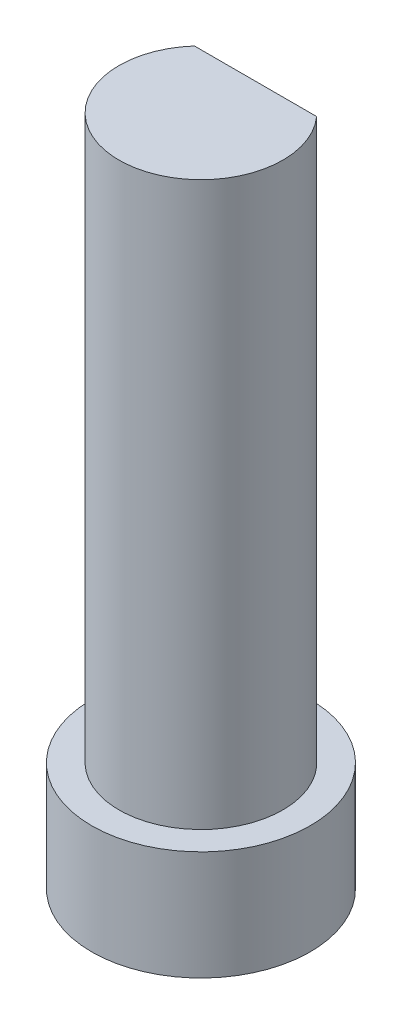
SolidWorks part; units mm, degrees
ref_plane "Alzado" through (0, 0, 0) normal (0, 0, 1) x (1, 0, 0)
ref_plane "Planta" through (0, 0, 0) normal (0, 1, 0) x (1, 0, 0)
ref_plane "Vista lateral" through (0, 0, 0) normal (1, 0, 0) x (0, 0, -1)
sketch "Croquis1" plane through (0, 0, 0) normal (0, 1, 0) x (1, 0, 0)
  circle A0 centre (0, 0) radius 2
extrude "Saliente-Extruir1" add sketch "Croquis1" along normal blind 2
sketch "Croquis2" plane through (0, 0, 0) normal (0, -1, 0) x (1, 0, 0)
  circle A0 centre (0, 0) radius 0.2
extrude "Cortar-Extruir1" cut sketch "Croquis2" against normal blind 2
sketch "Croquis3" plane through (0, 2, 0) normal (0, 1, 0) x (1, 0, 0)
  circle A0 centre (0, 0) radius 1.5
extrude "Saliente-Extruir2" add sketch "Croquis3" along normal blind 10.3 separate body
sketch "Croquis5" plane through (0, 12.3, 0) normal (0, 1, 0) x (1, 0, 0)
  line L0 (0, 0) -> (0, -1.5) construction
  line L1 (0, 0) -> (0, 1) construction
  line L2 (0, 1) -> (1.118, 1)
  line L3 (0, 1) -> (-1.118, 1)
  circle A0 centre (0, 0) radius 1.5 construction
  circle A2 centre (0, 0) radius 1.5
  arc A3 (1.118, 1) -> (-1.118, 1) centre (0, 0) ccw
  dimension "D1" = 0
extrude "Cortar-Extruir2" cut sketch "Croquis5" against normal blind 10.3
